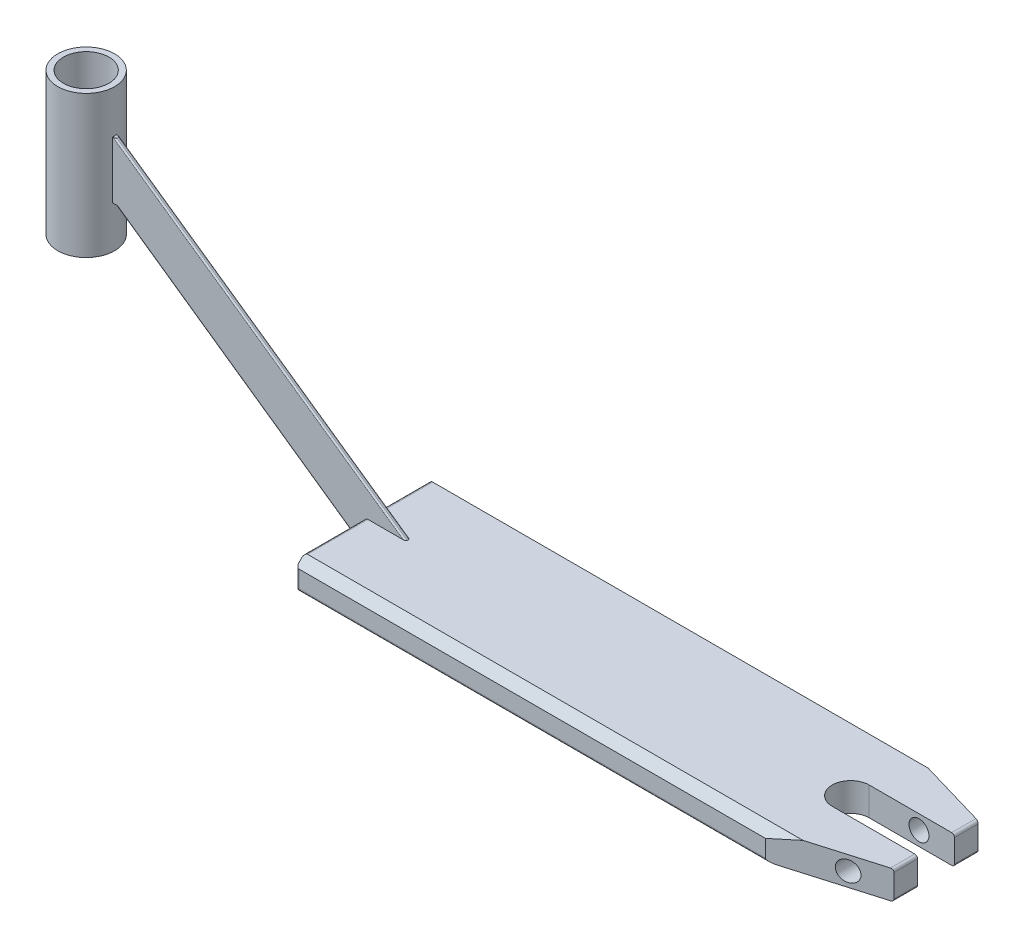
SolidWorks part; units mm, degrees
ref_plane "Front Plane" through (0, 0, 0) normal (0, 0, 1) x (1, 0, 0)
ref_plane "Top Plane" through (0, 0, 0) normal (0, 1, 0) x (1, 0, 0)
ref_plane "Right Plane" through (0, 0, 0) normal (1, 0, 0) x (0, 0, -1)
sketch "Sketch1" plane through (0, 0, 0) normal (0, 1, 0) x (1, 0, 0)
  circle A0 centre (0, 0) radius 16
  circle A1 centre (0, 0) radius 20
  dimension "D1" = 32
  dimension "D2" = 40
extrude "Boss-Extrude1" add sketch "Sketch1" along normal blind 100
ref_plane "Plane1" through (20, 0, 0) normal (1, 0, 0) x (0, 0, -1)
sketch "Sketch2" plane through (20, 0, 0) normal (1, 0, 0) x (0, 0, -1)
  line L0 (0, 102.6925) -> (0, -11.6389) construction
  line L1 (-20, 50) -> (20, 50) construction
  line L2 (-20, 100) -> (-20, 0) construction
  line L4 (1.5, 70) -> (-1.5, 70)
  line L5 (1.5, 70) -> (1.5, 30)
  line L6 (1.5, 30) -> (-1.5, 30)
  line L7 (-1.5, 70) -> (-1.5, 30)
  line L8 (1.5, 70) -> (-1.5, 30) construction
  line L9 (1.5, 30) -> (-1.5, 70) construction
  point P7 (0, 50)
  dimension "D1" = 3
  dimension "D2" = 40
extrude "Boss-Extrude11" add sketch "Sketch2" against normal blind 2
sketch "Sketch3" plane through (20, 0, 0) normal (1, 0, 0) x (0, 0, -1)
  line L0 (1.5, 30) -> (1.5, 70)
  line L1 (1.5, 70) -> (-1.5, 70)
  line L2 (-1.5, 70) -> (-1.5, 30)
  line L3 (-1.5, 30) -> (1.5, 30)
extrude "Boss-Extrude12" add sketch "Sketch3" along normal blind 2
sketch "Sketch4" plane through (0, 0, 1.5) normal (0, 0, 1) x (1, 0, 0)
  line L0 (22, 70) -> (254.7881, -93)
  line L1 (22, 70) -> (22, 30)
  line L2 (22, 30) -> (197.6622, -93)
  line L3 (197.6622, -93) -> (254.7881, -93)
  dimension "D1" = 145
  dimension "D2" = 35
  dimension "D3" = 163
extrude "Boss-Extrude13" add sketch "Sketch4" against normal blind 3
fillet "Fillet1" radius 1 6 edges at (22, 70, 0) (138.3941, -11.5, 1.5) (138.3941, -11.5, -1.5) (254.7881, -93, 0) (109.8311, -31.5, 1.5) (109.8311, -31.5, -1.5)
sketch "Sketch5" plane through (0, -93, 0) normal (0, -1, 0) x (1, 0, 0)
  line L0 (197.6622, -51.1347) -> (197.6622, -13.8024) construction
  line L1 (197.6622, 50) -> (197.6622, -50)
  line L2 (197.6622, -50) -> (597.6622, -50)
  line L3 (197.6622, 50) -> (597.6622, 50)
  line L4 (597.6622, 50) -> (597.6622, -50)
  line L6 (251.6165, 0) -> (-62.8345, 0) construction
  line L8 (251.6165, -1.5) -> (251.6165, 1.5) construction
  point P11 (197.6622, 0)
  point P12 (397.6622, -50)
  dimension "D1" = 100
  dimension "D2" = 400
  dimension "D3" = 397.6622
extrude "Boss-Extrude14" add sketch "Sketch5" against normal blind 20
fillet "Fillet2" radius 2 12 edges at (197.6622, -83, -50) (397.6622, -93, -50) (597.6622, -83, -50) (197.6622, -83, 50) (397.6622, -93, 50) (597.6622, -93, 0) (597.6622, -83, 50) (197.6622, -73, -25.75) (397.6622, -73, -50) (597.6622, -73, 0) (397.6622, -73, 50) (197.6622, -73, 25.75)
sketch "Sketch6" plane through (597.6622, 0, 0) normal (1, 0, 0) x (0, 0, -1)
  line L0 (-52, -81) -> (-42, -71)
  line L1 (-42, -71) -> (-52, -71)
  line L2 (-52, -71) -> (-52, -81)
  line L4 (-48, -75) -> (-48, -91) construction
  line L5 (48, -75) -> (-48, -75) construction
  dimension "D1" = 10
  dimension "D2" = 10
  dimension "D3" = 4
  dimension "D4" = 4
extrude "Cut-Extrude1" cut sketch "Sketch6" against normal through all both
sketch "Sketch7" plane through (597.6622, 0, 0) normal (1, 0, 0) x (0, 0, -1)
  line L0 (42, -71) -> (52, -81)
  line L1 (52, -81) -> (52, -71)
  line L2 (52, -71) -> (42, -71)
  line L3 (48, -91) -> (48, -75) construction
  line L4 (48, -75) -> (-46, -75) construction
  dimension "D1" = 10
  dimension "D2" = 10
  dimension "D3" = 4
  dimension "D4" = 4
extrude "Cut-Extrude2" cut sketch "Sketch7" against normal through all both
sketch "Sketch8" plane through (0, -73, 0) normal (0, 1, 0) x (1, 0, 0)
  line L0 (597.6622, 46) -> (597.6622, -46) construction
  line L1 (537.6622, 13) -> (597.6622, 13)
  line L3 (537.6622, -13) -> (597.6622, -13)
  line L4 (597.6622, 13) -> (597.6622, -13)
  line L5 (537.6622, 13) -> (597.6622, -13) construction
  line L6 (537.6622, -13) -> (597.6622, 13) construction
  line L10 (595.6622, -44) -> (199.6622, -44) construction
  arc A0 (537.6622, 13) -> (537.6622, -13) centre (537.6622, 0) ccw
  point P0 (567.6622, 0)
  dimension "D1" = 26
  dimension "D2" = 60
  dimension "D3" = 44
extrude "Cut-Extrude3" cut sketch "Sketch8" against normal through all
sketch "Sketch9" plane through (0, -73, 0) normal (0, 1, 0) x (1, 0, 0)
  line L1 (527.6622, 50) -> (597.6622, 50)
  line L2 (597.6622, 50) -> (597.6622, 29.5)
  line L5 (597.6622, 29.5) -> (527.6622, 50)
  line L6 (597.6622, 46) -> (597.6622, 13) construction
  line L7 (595.6622, 50) -> (199.6622, 50) construction
  dimension "D1" = 70
extrude "Cut-Extrude4" cut sketch "Sketch9" against normal through all
mirror "Mirror1" about plane through (0, 0, 0) normal (0, 0, 1) of "Cut-Extrude4"
sketch "Sketch11" plane through (0, 0, -13) normal (0, 0, 1) x (1, 0, 0)
  line L0 (597.6622, -91) -> (597.6622, -75) construction
  line L1 (548.15, -73) -> (595.6622, -73) construction
  circle A0 centre (572.6622, -83) radius 7
  dimension "D1" = 14
  dimension "D2" = 25
  dimension "D3" = 10
extrude "Cut-Extrude5" cut sketch "Sketch11" against normal through all both and the other way through all
